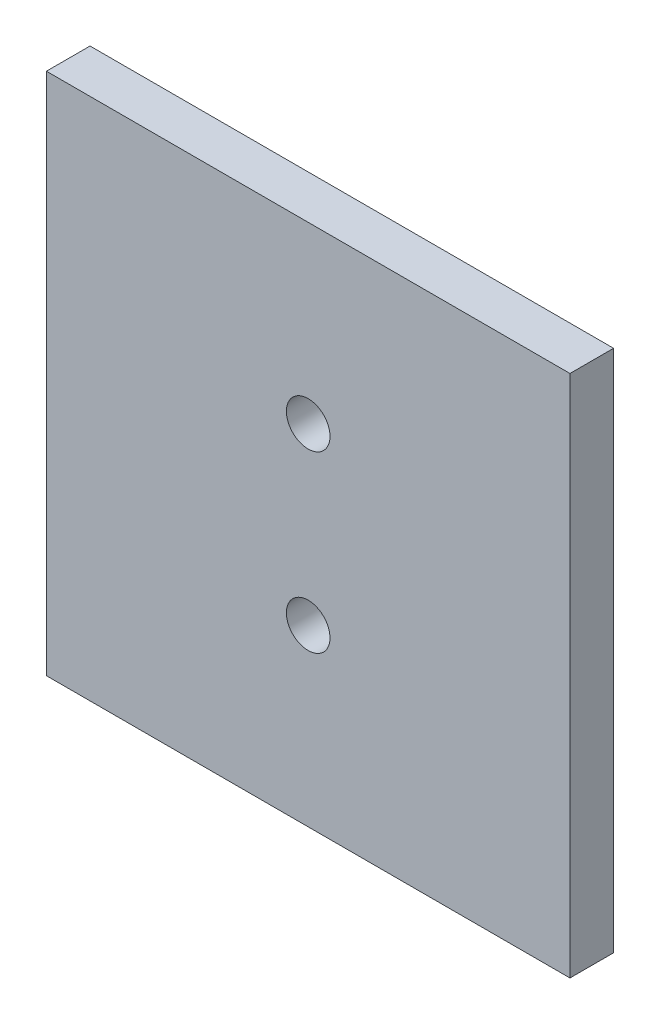
SolidWorks part; units mm, degrees
ref_plane "Front" through (0, 0, 0) normal (0, 0, 1) x (1, 0, 0)
ref_plane "Top" through (0, 0, 0) normal (0, 1, 0) x (1, 0, 0)
ref_plane "Right" through (0, 0, 0) normal (1, 0, 0) x (0, 0, -1)
sketch "Sketch1" plane through (0, 0, 0) normal (0, 0, 1) x (1, 0, 0)
  line L0 (0, 38.1) -> (76.2, 38.1) construction
  line L1 (0, 0) -> (76.2, 0)
  line L2 (0, 0) -> (0, 76.2)
  line L3 (0, 76.2) -> (76.2, 76.2)
  line L4 (76.2, 0) -> (76.2, 76.2)
  circle A0 centre (38.1, 50.8) radius 3.175
  circle A1 centre (38.1, 25.4) radius 3.175
  dimension "D3" = 38.1
  dimension "D5" = 6.35
  dimension "D1" = 76.2
  dimension "D2" = 76.2
  dimension "D4" = 25.4
extrude "Boss-Extrude1" add sketch "Sketch1" along normal blind 6.35
